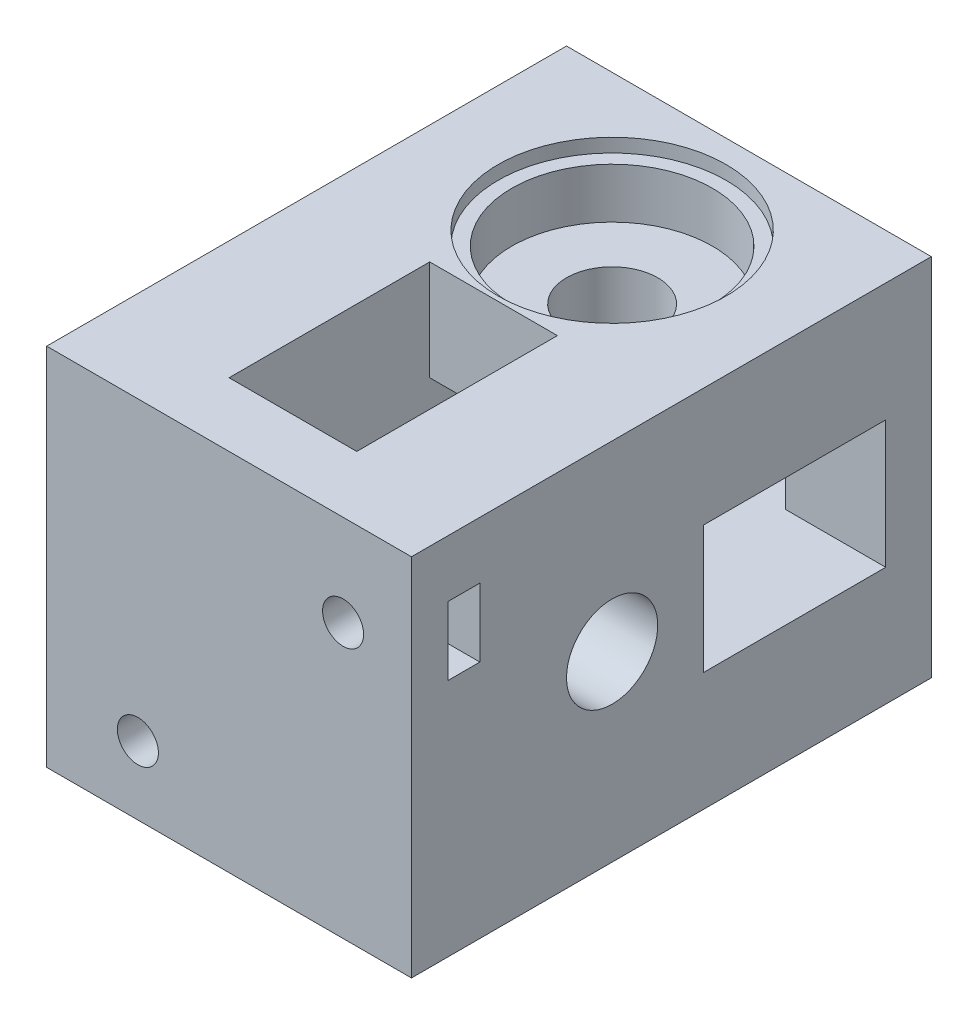
SolidWorks part; units mm, degrees
ref_plane "Plan de face" through (0, 0, 0) normal (0, 0, 1) x (1, 0, 0)
ref_plane "Plan de dessus" through (0, 0, 0) normal (0, 1, 0) x (1, 0, 0)
ref_plane "Plan de droite" through (0, 0, 0) normal (1, 0, 0) x (0, 0, -1)
sketch "Esquisse1" plane through (0, 0, 0) normal (0, 0, 1) x (1, 0, 0)
  line L1 (-40, 40) -> (0, 40)
  line L2 (-40, 40) -> (-40, 0)
  line L3 (-40, 0) -> (0, 0)
  line L4 (0, 40) -> (0, 0)
  dimension "D1" = 40
  dimension "D2" = 40
extrude "Boss.-Extru.1" add sketch "Esquisse1" along normal blind 50
sketch "Esquisse2" plane through (0, 40, 0) normal (0, 1, 0) x (1, 0, 0)
  line L0 (0, 0) -> (-40, 0) construction
  line L1 (-40, -50) -> (-40, 0) construction
  circle A0 centre (-20, -15) radius 5
  dimension "D1" = 10
  dimension "D2" = 15
  dimension "D3" = 20
extrude "Enlèv. mat.-Extru.1" cut sketch "Esquisse2" against normal through all
sketch "Esquisse3" plane through (-40, 0, 0) normal (-1, 0, 0) x (0, 0, 1)
  line L0 (50, 40) -> (50, 0) construction
  line L1 (50, 40) -> (0, 40) construction
  circle A0 centre (35, 20) radius 5
  dimension "D1" = 10
  dimension "D2" = 15
  dimension "D3" = 20
extrude "Enlèv. mat.-Extru.2" cut sketch "Esquisse3" against normal through all
sketch "Esquisse4" plane through (-40, 0, 0) normal (-1, 0, 0) x (0, 0, 1)
  line L1 (22, 27) -> (0, 27)
  line L2 (22, 27) -> (22, 13)
  line L3 (22, 13) -> (0, 13)
  line L4 (0, 27) -> (0, 13)
  line L5 (0, 40) -> (0, 0) construction
  line L6 (50, 0) -> (0, 0) construction
  line L7 (50, 40) -> (0, 40) construction
  dimension "D1" = 14
  dimension "D2" = 22
  dimension "D3" = 0
  dimension "D4" = 13
  dimension "D5" = 13
extrude "Enlèv. mat.-Extru.3" cut sketch "Esquisse4" against normal blind 29
sketch "Esquisse5" plane through (0, 0, 0) normal (0, -1, 0) x (1, 0, 0)
  line L0 (-40, 50) -> (0, 50) construction
  line L1 (-13, 25) -> (-27, 25)
  line L2 (-13, 25) -> (-13, 45)
  line L3 (-13, 45) -> (-27, 45)
  line L4 (-27, 25) -> (-27, 45)
  line L5 (-40, 50) -> (-40, 0) construction
  dimension "D1" = 20
  dimension "D2" = 5
  dimension "D3" = 14
  dimension "D4" = 13
extrude "Enlèv. mat.-Extru.4" cut sketch "Esquisse5" against normal blind 29
sketch "Esquisse6" plane through (0, 0, 0) normal (1, 0, 0) x (0, 0, -1)
  line L1 (-5, 27) -> (-25, 27)
  line L2 (0, 0) -> (0, 40) construction
  line L3 (-5, 13) -> (-25, 13)
  line L4 (-25, 27) -> (-25, 13)
  line L5 (-50, 0) -> (0, 0) construction
  line L6 (-5, 27) -> (-5, 13)
  dimension "D1" = 14
  dimension "D2" = 5
  dimension "D3" = 13
  dimension "D4" = 20
extrude "Enlèv. mat.-Extru.5" cut sketch "Esquisse6" against normal blind 24
sketch "Esquisse7" plane through (0, 40, 0) normal (0, 1, 0) x (1, 0, 0)
  line L0 (0, -50) -> (-40, -50) construction
  line L1 (-27, -50) -> (-13, -50)
  line L2 (-27, -50) -> (-27, -28)
  line L3 (-27, -28) -> (-13, -28)
  line L4 (-13, -50) -> (-13, -28)
  line L5 (-40, -50) -> (-40, 0) construction
  dimension "D1" = 14
  dimension "D2" = 22
  dimension "D3" = 13
extrude "Enlèv. mat.-Extru.6" cut sketch "Esquisse7" against normal blind 24
sketch "Esquisse10" plane through (0, 40, 0) normal (0, 1, 0) x (1, 0, 0)
  circle A0 centre (-20, -15) radius 11
  dimension "D1" = 22
extrude "Enlèv. mat.-Extru.9" cut sketch "Esquisse10" against normal blind 7
sketch "Esquisse11" plane through (0, 40, 0) normal (0, 1, 0) x (1, 0, 0)
  circle A0 centre (-20, -15) radius 12.5
  dimension "D1" = 25
extrude "Enlèv. mat.-Extru.10" cut sketch "Esquisse11" against normal blind 1.5
sketch "Esquisse14" plane through (-40, 0, 0) normal (-1, 0, 0) x (0, 0, 1)
  circle A0 centre (35, 20) radius 11
  dimension "D1" = 22
extrude "Enlèv. mat.-Extru.11" cut sketch "Esquisse14" against normal blind 7
sketch "Esquisse15" plane through (-40, 0, 0) normal (-1, 0, 0) x (0, 0, 1)
  circle A0 centre (35, 20) radius 12.5
  dimension "D1" = 25
extrude "Enlèv. mat.-Extru.12" cut sketch "Esquisse15" against normal blind 1.5
sketch "Esquisse16" plane through (0, 0, 50) normal (0, 0, 1) x (1, 0, 0)
  line L1 (0, 0) -> (-40, 0)
  line L2 (0, 0) -> (0, 40)
  line L3 (0, 40) -> (-40, 40)
  line L4 (-40, 0) -> (-40, 40)
extrude "Boss.-Extru.2" add sketch "Esquisse16" along normal blind 7
sketch "Esquisse17" plane through (0, 0, 57) normal (0, 0, 1) x (1, 0, 0)
  line L0 (-40, 40) -> (-40, 0) construction
  line L1 (0, 40) -> (-40, 40) construction
  circle A0 centre (-30, 7.5) radius 2.25
  circle A1 centre (-7.5, 30) radius 2.25
  dimension "D1" = 4.5
  dimension "D2" = 4.5
  dimension "D3" = 10
  dimension "D4" = 10
  dimension "D5" = 32.5
  dimension "D6" = 32.5
extrude "Enlèv. mat.-Extru.13" cut sketch "Esquisse17" against normal blind 15
sketch "Esquisse18" plane through (0, 0, 0) normal (0, -1, 0) x (1, 0, 0)
  line L0 (-40, 57) -> (0, 57) construction
  line L1 (-26.5, 50) -> (-33.5, 50)
  line L2 (-26.5, 50) -> (-26.5, 53)
  line L3 (-26.5, 53) -> (-33.5, 53)
  line L4 (-33.5, 50) -> (-33.5, 53)
  line L5 (-40, 57) -> (-40, 0) construction
  dimension "D1" = 7
  dimension "D2" = 3
  dimension "D3" = 4
  dimension "D4" = 6.5
extrude "Enlèv. mat.-Extru.14" cut sketch "Esquisse18" against normal blind 12
sketch "Esquisse19" plane through (0, 0, 0) normal (1, 0, 0) x (0, 0, -1)
  line L0 (-57, 0) -> (-57, 40) construction
  line L1 (-49.5, 33.75) -> (-53, 33.75)
  line L2 (-49.5, 33.75) -> (-49.5, 26.25)
  line L3 (-49.5, 26.25) -> (-53, 26.25)
  line L4 (-53, 33.75) -> (-53, 26.25)
  line L5 (-57, 40) -> (0, 40) construction
  dimension "D1" = 7.5
  dimension "D2" = 3.5
  dimension "D3" = 4
  dimension "D4" = 6.25
extrude "Enlèv. mat.-Extru.15" cut sketch "Esquisse19" against normal blind 12
